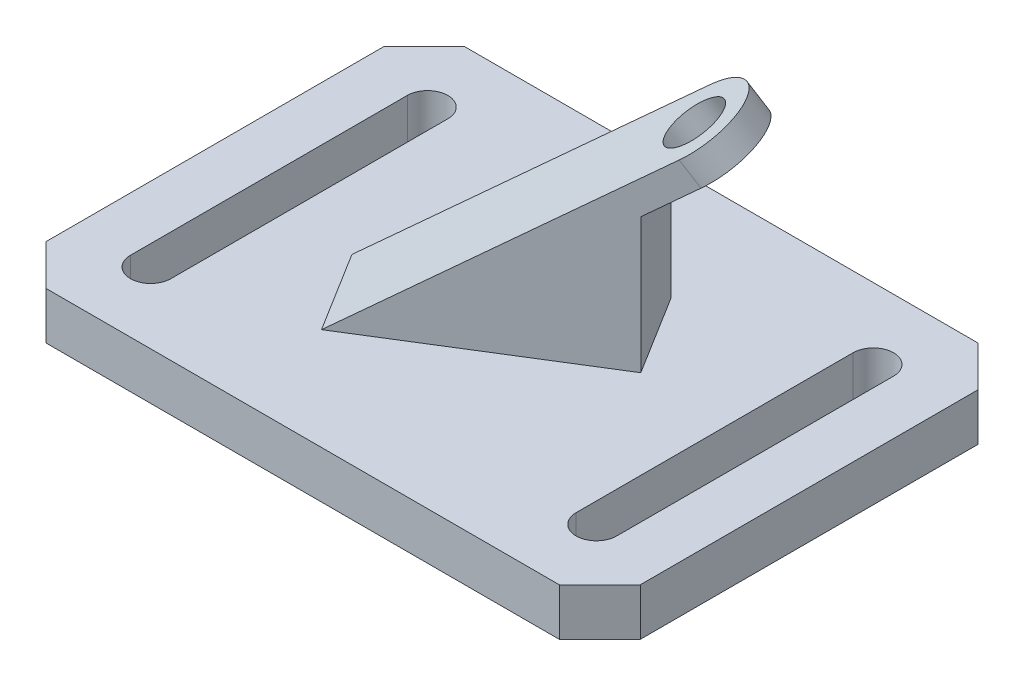
SolidWorks part; units mm, degrees
ref_plane "Front Plane" through (0, 0, 0) normal (0, 0, 1) x (1, 0, 0)
ref_plane "Top Plane" through (0, 0, 0) normal (0, 1, 0) x (1, 0, 0)
ref_plane "Right Plane" through (0, 0, 0) normal (1, 0, 0) x (0, 0, -1)
sketch "Sketch1" plane through (0, 0, 0) normal (0, 1, 0) x (1, 0, 0)
  line L0 (-44, 25) -> (-38, 31)
  line L1 (-38, -31) -> (38, -31)
  line L2 (-44, -25) -> (-44, 25)
  line L3 (-38, 31) -> (38, 31)
  line L4 (44, -25) -> (44, 25)
  line L5 (-44, -31) -> (44, 31) construction
  line L6 (-44, 31) -> (44, -31) construction
  line L7 (38, 31) -> (44, 25)
  line L8 (38, -31) -> (44, -25)
  line L9 (-44, -25) -> (-38, -31)
  line L10 (0, 0) -> (0, 43.5111) construction
  line L11 (0, 0) -> (-33, 0) construction
  line L12 (-33, -20.5) -> (-33, 20.5) construction
  line L13 (-36, -20.5) -> (-36, 20.5)
  line L14 (-30, -20.5) -> (-30, 20.5)
  line L15 (33, -20.5) -> (33, 20.5) construction
  line L16 (36, -20.5) -> (36, 20.5)
  line L17 (30, -20.5) -> (30, 20.5)
  arc A0 (-36, -20.5) -> (-30, -20.5) centre (-33, -20.5) ccw
  arc A1 (-30, 20.5) -> (-36, 20.5) centre (-33, 20.5) ccw
  arc A2 (36, -20.5) -> (30, -20.5) centre (33, -20.5) cw
  arc A3 (30, 20.5) -> (36, 20.5) centre (33, 20.5) cw
  point P0 (0, 0)
  point P19 (-33, 0)
  point P26 (33, 0)
  dimension "D3" = 3
  dimension "D1" = 88
  dimension "D2" = 62
  dimension "D4" = 8
  dimension "D5" = 41
extrude "Boss-Extrude1" add sketch "Sketch1" along normal blind 7
sketch "Sketch2" plane through (0, 7, 0) normal (0, 1, 0) x (1, 0, 0)
  line L0 (-33, -20.5) -> (33, 20.5) construction
  point P4 (0, 0)
ref_plane "Plane1" through (0, 0, 0) normal (0.5277, 0, 0.8494) x (0.8494, 0, -0.5277)
sketch "Sketch3" plane through (0, 0, 0) normal (0.5277, 0, 0.8494) x (0.8494, 0, -0.5277)
  line L0 (-18.8491, 7) -> (25.2679, 39.0528)
  line L1 (-38.8491, 7) -> (38.8491, 7) construction
  line L2 (25.2679, 39.0528) -> (27.619, 35.8168)
  line L3 (27.619, 35.8168) -> (15.4838, 27)
  line L4 (15.4838, 27) -> (15.4838, 7)
  line L5 (15.4838, 7) -> (-18.8491, 7)
  line L6 (-18.8491, 7) -> (-38.8491, 7)
  line L7 (25.2679, 39.0528) -> (13.9417, 30.8239) construction
  line L8 (13.9417, 30.8239) -> (25.2679, 39.0528) construction
  line L9 (13.9417, 30.8239) -> (25.2679, 39.0528) construction
  line L10 (19.6048, 34.9383) -> (20.976, 33.051) construction
  dimension "D1" = 20
  dimension "D2" = 4
  dimension "D3" = 20
  dimension "D4" = 36
  dimension "D5" = 14
  dimension "D6" = 8
extrude "Boss-Extrude2" add sketch "Sketch3" against normal mid plane 14 contours L5 L4 L3 L2 L0
sketch "Sketch4" plane through (-8.3593, 13.5448, 5.1929) normal (-0.4993, 0.809, 0.3102) x (0.8664, 0.4662, 0.1787)
  line L0 (30.157, 31.9819) -> (38.6834, 20.8778) construction
  line L1 (-13.0947, -1.2293) -> (30.157, 31.9819) construction
  line L2 (-4.5683, -12.3334) -> (38.6834, 20.8778) construction
  line L7 (-4.5683, -12.3334) -> (38.6834, 20.8778)
  line L8 (38.6834, 20.8778) -> (30.157, 31.9819)
  line L9 (30.157, 31.9819) -> (-13.0947, -1.2293)
  line L10 (-13.0947, -1.2293) -> (-4.5683, -12.3334)
  line L11 (33.1313, 16.6146) -> (38.6834, 20.8778)
  line L12 (38.6834, 20.8778) -> (30.157, 31.9819)
  line L13 (30.157, 31.9819) -> (24.6049, 27.7187)
  line L14 (-13.0947, -1.2293) -> (-4.5683, -12.3334)
  arc A0 (33.1313, 16.6146) -> (24.6049, 27.7187) centre (28.8681, 22.1667) ccw
  circle A1 centre (28.8681, 22.1667) radius 4
  line M5 (-4.5683, -12.3334) -> (38.6834, 20.8778)
  line M6 (38.6834, 20.8778) -> (30.157, 31.9819)
  line M7 (30.157, 31.9819) -> (-13.0947, -1.2293)
  dimension "D2" = 8
  dimension "D1" = 0
extrude "Cut-Extrude1" cut sketch "Sketch4" against normal blind 14 and the other way through all contours A1 | A0 L12 M7 | A0 M5 M6
